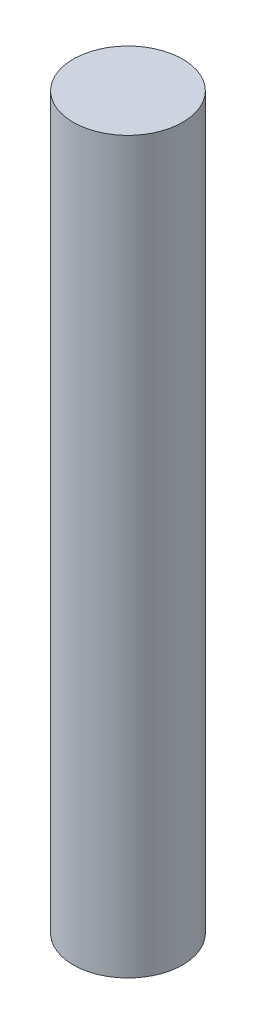
SolidWorks part; units mm, degrees
ref_plane "Front Plane" through (0, 0, 0) normal (0, 0, 1) x (1, 0, 0)
ref_plane "Top Plane" through (0, 0, 0) normal (0, 1, 0) x (1, 0, 0)
ref_plane "Right Plane" through (0, 0, 0) normal (1, 0, 0) x (0, 0, -1)
sketch "Sketch1" plane through (0, 0, 0) normal (0, 1, 0) x (1, 0, 0)
  circle A0 centre (0, 0) radius 3
  dimension "D1" = 6
extrude "Boss-Extrude1" add sketch "Sketch1" along normal mid plane 40
